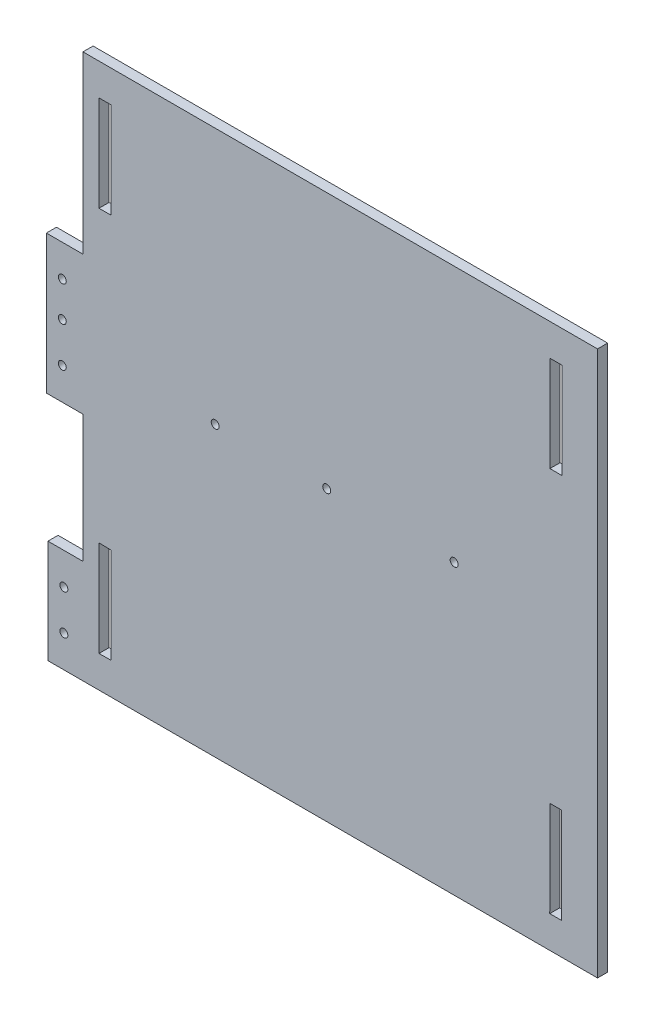
SolidWorks part; units mm, degrees
material "Cedar"
ref_plane "Front Plane" through (0, 0, 0) normal (0, 0, 1) x (1, 0, 0)
ref_plane "Top Plane" through (0, 0, 0) normal (0, 1, 0) x (1, 0, 0)
ref_plane "Right Plane" through (0, 0, 0) normal (1, 0, 0) x (0, 0, -1)
sketch "Model" plane through (0, 0, 0) normal (0, 0, 1) x (1, 0, 0)
  line L0 (691.8406, 302.6115) -> (346.8406, 302.6115)
  line L1 (691.8406, 302.6115) -> (691.8406, 644.6115)
  line L2 (368.8406, 644.6115) -> (368.8406, 534.6115)
  line L3 (368.8406, 447.6115) -> (368.8406, 367.6115)
  line L4 (346.8406, 302.6115) -> (346.8406, 367.6115)
  line L5 (346.8406, 367.6115) -> (368.8406, 367.6115)
  line L6 (368.8406, 447.6115) -> (345.8406, 447.6115)
  line L7 (345.8406, 447.6115) -> (345.8406, 534.6115)
  line L8 (378.8782, 624.6071) -> (386.3782, 624.6071)
  line L9 (386.3782, 624.6071) -> (386.3782, 564.607)
  line L10 (386.3782, 564.607) -> (378.8782, 564.607)
  line L11 (378.8782, 564.607) -> (378.8782, 624.6071)
  line L12 (378.8782, 382.6751) -> (386.377, 382.5389)
  line L13 (386.377, 382.5389) -> (386.377, 322.6326)
  line L14 (386.377, 322.6326) -> (378.8782, 322.5479)
  line L15 (378.8782, 322.5479) -> (378.8782, 382.6751)
  line L16 (661.9873, 624.6115) -> (669.4873, 624.6115)
  line L17 (669.4873, 624.6115) -> (669.4591, 564.6115)
  line L18 (669.4591, 564.6115) -> (661.9591, 564.6115)
  line L19 (661.9591, 564.6115) -> (661.9873, 624.6115)
  line L20 (661.8734, 382.6148) -> (669.3734, 382.6112)
  line L21 (669.3734, 382.6112) -> (669.3451, 322.6112)
  line L22 (669.3451, 322.6112) -> (661.8451, 322.6148)
  line L23 (661.8451, 322.6148) -> (661.8734, 382.6148)
  line L24 (345.8406, 534.6115) -> (368.8406, 534.6115)
  line L25 (691.8406, 644.6115) -> (368.8406, 644.6115)
  circle A0 centre (355.8406, 514.6115) radius 2.5
  circle A1 centre (355.8406, 492.6115) radius 2.5
  circle A2 centre (355.8406, 467.6115) radius 2.5
  circle A3 centre (356.8406, 347.6115) radius 2.5
  circle A4 centre (356.8406, 322.6115) radius 2.5
  circle A5 centre (451.8406, 483.6115) radius 2.5
  circle A6 centre (521.8406, 483.6115) radius 2.5
  circle A7 centre (601.8406, 483.6115) radius 2.5
extrude "Boss-Extrude1" add sketch "Model" against normal blind 6.35
